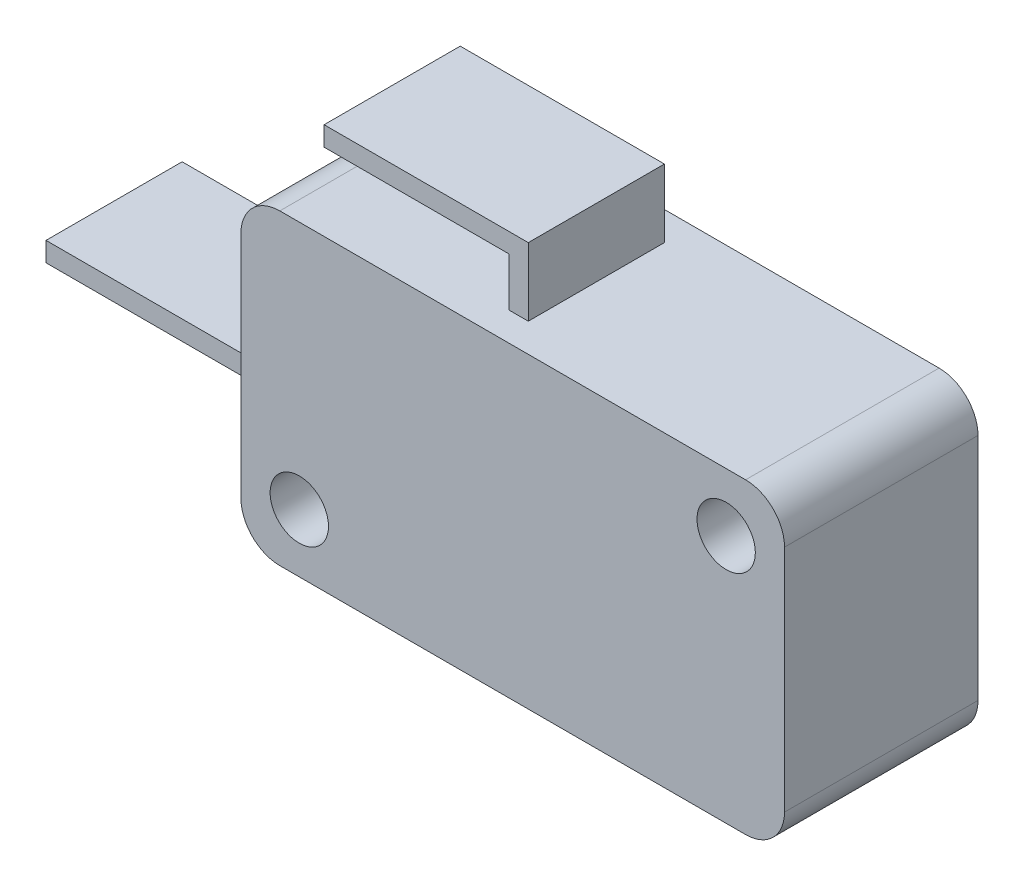
SolidWorks part; units mm, degrees
ref_plane "Front Plane" through (0, 0, 0) normal (0, 0, 1) x (1, 0, 0)
ref_plane "Top Plane" through (0, 0, 0) normal (0, 1, 0) x (1, 0, 0)
ref_plane "Right Plane" through (0, 0, 0) normal (1, 0, 0) x (0, 0, -1)
sketch "Sketch1" plane through (0, 0, 0) normal (0, 0, 1) x (1, 0, 0)
  line L1 (-13.975, 7.9) -> (13.975, 7.9)
  line L2 (-13.975, 7.9) -> (-13.975, -7.9)
  line L3 (-13.975, -7.9) -> (13.975, -7.9)
  line L4 (13.975, 7.9) -> (13.975, -7.9)
  point P4 (13.975, 0)
  point P6 (0, 7.9)
  dimension "D1" = 27.95
  dimension "D2" = 15.8
extrude "Extrude1" add sketch "Sketch1" along normal blind 9.95
sketch "Sketch2" plane through (0, 0, 9.95) normal (0, 0, 1) x (1, 0, 0)
  line L0 (13.975, 7.9) -> (-13.975, 7.9) construction
  line L1 (-13.975, 7.9) -> (-13.975, -7.9) construction
  line L2 (-13.975, -7.9) -> (13.975, -7.9) construction
  line L3 (13.975, -7.9) -> (13.975, 7.9) construction
  circle A0 centre (10.975, 4.9) radius 1.5
  circle A1 centre (-10.975, -4.9) radius 1.5
  dimension "D1" = 3
  dimension "D3" = 3
  dimension "D2" = 3
  dimension "D4" = 3
  dimension "D5" = 3
  dimension "D6" = 3
extrude "Extrude2" cut sketch "Sketch2" against normal through all
fillet "Fillet1" radius 2 4 edges at (-13.975, -7.9, 4.975) (13.975, -7.9, 4.975) (-13.975, 7.9, 4.975) (13.975, 7.9, 4.975)
sketch "Sketch3" plane through (-13.975, 0, 0) normal (-1, 0, 0) x (0, 0, 1)
  line L0 (9.95, -7.9) -> (0, -7.9) construction
  line L1 (1.475, -0.9) -> (8.475, -0.9)
  line L2 (1.475, -0.9) -> (1.475, -1.9)
  line L3 (1.475, -1.9) -> (8.475, -1.9)
  line L4 (8.475, -0.9) -> (8.475, -1.9)
  line L6 (4.975, 5.9) -> (4.975, -5.9) construction
  line L7 (9.95, 5.9) -> (0, 5.9) construction
  line L8 (0, -5.9) -> (9.95, -5.9) construction
  point P12 (4.975, -1.9)
  dimension "D1" = 7
  dimension "D2" = 1
  dimension "D3" = 6
extrude "Extrude3" add sketch "Sketch3" along normal blind 11.5
sketch "Sketch4" plane through (0, 7.9, 0) normal (0, 1, 0) x (-1, 0, 0)
  line L0 (13.975, 9.95) -> (13.975, 0) construction
  line L1 (1.675, 1.475) -> (0.675, 1.475)
  line L2 (1.675, 1.475) -> (1.675, 8.475)
  line L3 (1.675, 8.475) -> (0.675, 8.475)
  line L4 (0.675, 1.475) -> (0.675, 8.475)
  line L5 (11.975, 4.975) -> (-11.975, 4.975) construction
  line L6 (11.975, 0) -> (11.975, 9.95) construction
  line L7 (-11.975, 9.95) -> (-11.975, 0) construction
  point P12 (0.675, 4.975)
  dimension "D1" = 1
  dimension "D2" = 7
  dimension "D3" = 13.3
extrude "Extrude4" add sketch "Sketch4" along normal blind 3.5
sketch "Sketch5" plane through (-1.675, 0, 0) normal (-1, 0, 0) x (0, 0, 1)
  line L0 (8.475, 11.4) -> (8.475, 7.9) construction
  line L1 (1.475, 11.4) -> (8.475, 11.4)
  line L2 (1.475, 11.4) -> (1.475, 10.4)
  line L3 (1.475, 10.4) -> (8.475, 10.4)
  line L4 (8.475, 11.4) -> (8.475, 10.4)
  dimension "D1" = 1
extrude "Extrude5" add sketch "Sketch5" along normal blind 9.5
sketch "Sketch6" plane through (0, -7.9, 0) normal (0, -1, 0) x (1, 0, 0)
  line L0 (13.975, 9.95) -> (13.975, 0) construction
  line L1 (9.575, 6.975) -> (6.975, 6.975)
  line L2 (9.575, 6.975) -> (9.575, 2.975)
  line L3 (9.575, 2.975) -> (6.975, 2.975)
  line L4 (6.975, 6.975) -> (6.975, 2.975)
  line L5 (11.975, 4.975) -> (-11.975, 4.975) construction
  line L6 (11.975, 0) -> (11.975, 9.95) construction
  line L7 (-11.975, 9.95) -> (-11.975, 0) construction
  point P12 (6.975, 4.975)
  dimension "D1" = 4
  dimension "D2" = 2.6
  dimension "D3" = 7
extrude "Extrude6" cut sketch "Sketch6" against normal blind 3
sketch "Sketch7" plane through (0, -7.9, 0) normal (0, -1, 0) x (1, 0, 0)
  line L0 (13.975, 9.95) -> (13.975, 0) construction
  line L1 (-1.525, 7.3323) -> (-2.525, 7.3323)
  line L2 (-1.525, 7.3323) -> (-1.525, 3.496)
  line L3 (-1.525, 3.496) -> (-2.525, 3.496)
  line L4 (-2.525, 7.3323) -> (-2.525, 3.496)
  dimension "D1" = 15.5
  dimension "D2" = 1
extrude "Extrude7" cut sketch "Sketch7" against normal blind 3
sketch "Sketch8" plane through (0, 0, 7.3323) normal (0, 0, -1) x (-1, 0, 0)
  line L0 (1.525, -4.9) -> (2.525, -4.9) construction
  line L1 (1.525, -4.9) -> (1.525, -7.9) construction
  circle A0 centre (2.025, -5.4) radius 0.25
  dimension "D1" = 0.5
  dimension "D2" = 0.5
  dimension "D3" = 0.5
extrude "Extrude8" cut sketch "Sketch8" against normal blind 1
